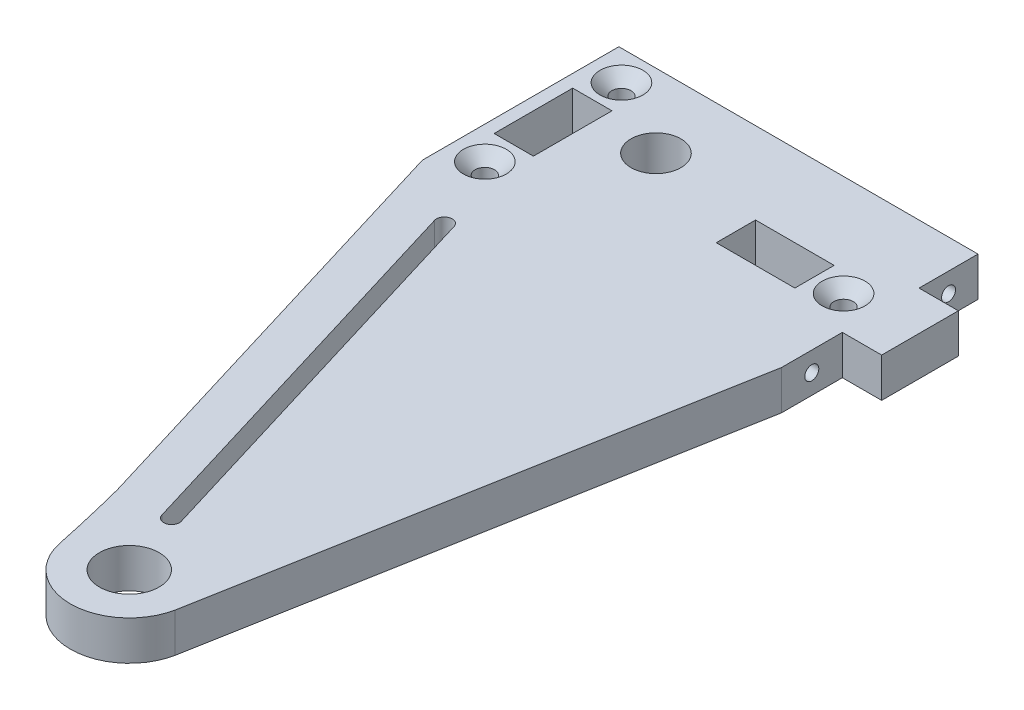
SolidWorks part; units mm, degrees
ref_plane "Front Plane" through (0, 0, 0) normal (0, 0, 1) x (1, 0, 0)
ref_plane "Top Plane" through (0, 0, 0) normal (0, 1, 0) x (1, 0, 0)
ref_plane "Right Plane" through (0, 0, 0) normal (1, 0, 0) x (0, 0, -1)
sketch "Sketch1" plane through (0, 0, 0) normal (0, 1, 0) x (1, 0, 0)
  line L0 (0, 0) -> (0, 112.776) construction
  line L1 (24.384, 112.776) -> (-30.48, 112.776) construction
  line L2 (24.384, 81.026) -> (9.3228, -1.9523)
  line L3 (24.384, 112.776) -> (24.384, 103.251)
  line L4 (24.384, 112.776) -> (-30.48, 112.776)
  line L5 (-30.48, 112.776) -> (-33.655, 112.776) construction
  line L6 (-33.655, 112.776) -> (-33.655, 81.026)
  line L7 (-30.48, 112.776) -> (-33.655, 112.776)
  line L8 (24.384, 103.251) -> (30.734, 103.251)
  line L9 (-33.655, 81.026) -> (-12.1847, 10.2842)
  line L10 (24.384, 90.8558) -> (30.734, 90.8558)
  line L11 (30.734, 103.251) -> (30.734, 90.8558)
  line L12 (14.3442, 96.393) -> (45.8369, 96.393) construction
  line L13 (19.0432, 100.6942) -> (19.0432, 92.8952) construction
  line L14 (-5.0329, 10.2842) -> (-24.2431, 73.579)
  line L15 (1.6442, 99.568) -> (1.6442, 93.218)
  line L16 (1.6442, 99.568) -> (14.3442, 99.568)
  line L17 (14.3442, 99.568) -> (14.3442, 93.218)
  line L18 (-28.3943, 85.857) -> (-28.4151, 107.9549) construction
  line L19 (-25.2401, 103.251) -> (-31.5901, 103.251)
  line L20 (-25.2401, 103.251) -> (-25.2401, 90.551)
  line L21 (-25.2401, 90.551) -> (-31.5901, 90.551)
  line L22 (-31.5901, 103.251) -> (-31.5901, 90.551)
  line L23 (1.6442, 93.218) -> (14.3442, 93.218)
  line L24 (-2.6024, 11.0218) -> (-21.8125, 74.3167)
  line L25 (24.384, 81.026) -> (24.384, 90.8558)
  circle A0 centre (0, 0) radius 77.47 construction
  circle A1 centre (0, 0) radius 4.826
  arc A2 (-9.3228, -1.9523) -> (9.3228, -1.9523) centre (0, 0) ccw
  circle A3 centre (-28.4151, 107.9549) radius 1.5621
  circle A4 centre (-28.3943, 85.857) radius 1.5621
  circle A5 centre (-15.748, 100.8634) radius 4.0386
  arc A6 (-21.8125, 74.3167) -> (-24.2431, 73.579) centre (-23.0278, 73.9479) ccw
  arc A7 (-12.1847, 10.2842) -> (-9.3228, -1.9523) centre (-273.0562, -57.1826) cw
  circle A8 centre (19.0432, 96.393) radius 1.5621
  arc A9 (-5.0329, 10.2842) -> (-2.6024, 11.0218) centre (-3.8177, 10.653) ccw
  dimension "D1" = 154.94
  dimension "D2" = 9.652
  dimension "D3" = 19.05
  dimension "D14" = 3.1242
  dimension "D15" = 8.0772
  dimension "D7" = 2.54
  dimension "D4" = 112.776
  dimension "D5" = 6.35
  dimension "D6" = 12.3952
  dimension "D8" = 9.525
  dimension "D9" = 6.35
  dimension "D10" = 12.7
  dimension "D11" = 13.208
  dimension "D12" = 5.5372
  dimension "D13" = 6.35
  dimension "D16" = 15.748
  dimension "D17" = 11.9126
  dimension "D18" = 12.7
extrude "Boss-Extrude1" add sketch "Sketch1" along normal blind 6.35
sketch "Sketch2" plane through (24.384, 0, 0) normal (1, 0, 0) x (0, 0, -1)
  line L0 (103.251, 3.175) -> (112.776, 3.175) construction
  line L1 (108.0135, 0) -> (108.0135, 6.35) construction
  line L2 (96.9645, 6.35) -> (96.9645, 0) construction
  circle A0 centre (108.0135, 3.175) radius 1.1303
  circle A1 centre (85.9155, 3.175) radius 1.1303
  dimension "D1" = 2.2606
extrude "Cut-Extrude1" cut sketch "Sketch2" against normal blind 12.7
chamfer "Chamfer1" distance 1.905 angle 45 3 edges at (19.0432, 6.35, -97.9551) (-28.3943, 6.35, -87.4191) (-28.4151, 6.35, -106.3928)
